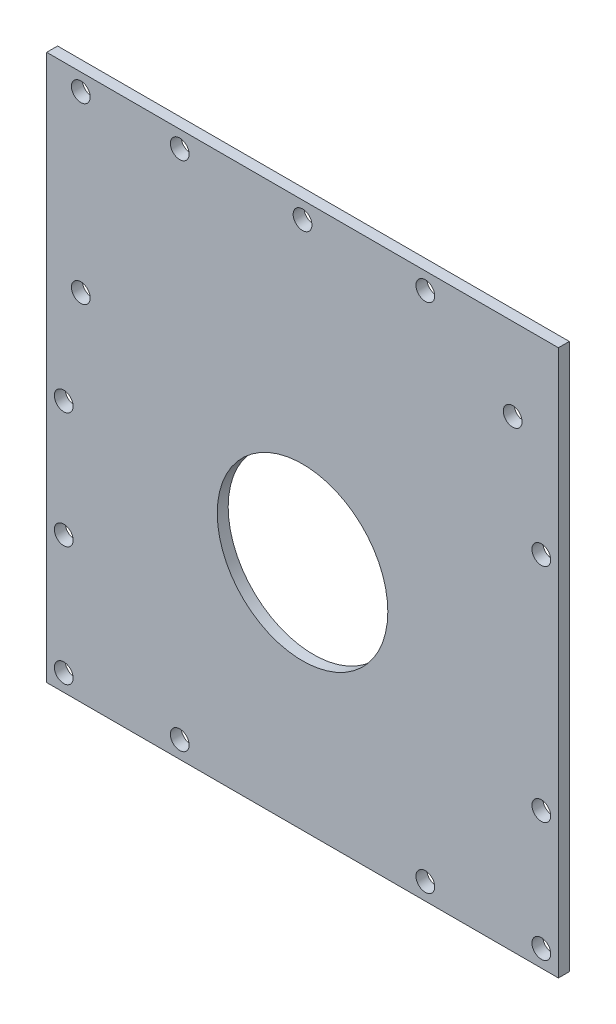
SolidWorks part; units mm, degrees
material "AISI 304"
ref_plane "Front Plane" through (0, 0, 0) normal (0, 0, 1) x (1, 0, 0)
ref_plane "Top Plane" through (0, 0, 0) normal (0, 1, 0) x (1, 0, 0)
ref_plane "Right Plane" through (0, 0, 0) normal (1, 0, 0) x (0, 0, -1)
sketch "Sketch1" plane through (0, 0, 0) normal (0, 0, 1) x (1, 0, 0)
  line L0 (-75, 80) -> (75, -80) construction
  line L1 (-75, 80) -> (75, 80)
  line L2 (-75, 80) -> (-75, -80)
  line L3 (-75, -80) -> (75, -80)
  line L4 (75, 80) -> (75, -80)
  point P0 (0, 0)
  point P6 (0, 0)
  dimension "D1" = 150
  dimension "D2" = 160
extrude "Boss-Extrude1" add sketch "Sketch1" along normal blind 3.2
sketch "Sketch2" plane through (0, 0, 3.2) normal (0, 0, 1) x (1, 0, 0)
  line L0 (0, -12) -> (0, -47.5) construction
  line L3 (-75, -80) -> (75, -80) construction
  circle A1 centre (0, -12) radius 25
  dimension "D1" = 35.5
  dimension "D3" = 25
  dimension "D4" = 68
extrude "Cut-Extrude1" cut sketch "Sketch2" against normal up to next
sketch "Sketch4" plane through (0, 0, 3.2) normal (0, 0, 1) x (1, 0, 0)
  line L1 (-75, 68.5917) -> (-2.1136, 63.6666) construction
  line L3 (-15.844, 37.0022) -> (-75, 32.3611) construction
  line L4 (-18.745, 35.9674) -> (-15.844, 37.0022) construction
  spline S1 degree 3 poles (-2.1136, 63.6666) (2.6479, 63.5435) (7.3732, 62.9696) (16.586, 60.9588) (21.0732, 59.5219) (29.6553, 55.8535) (33.75, 53.622) (41.4098, 48.4598) (44.9747, 45.5292) (51.4594, 39.0872) (54.379, 35.5759) (59.4827, 28.1094) (61.6668, 24.1543) (65.2376, 15.9498) (66.6242, 11.7006) (68.5678, 3.0651) (69.1247, -1.321) (69.407, -10.0716) (69.1323, -14.4359) (67.7793, -22.9884) (66.701, -27.1763) (63.7966, -35.2312) (61.9706, -39.0979) (57.6525, -46.38) (55.1604, -49.7953) (49.6136, -56.0632) (46.5591, -58.9158) (40.0087, -63.9697) (36.513, -66.1711) (29.2148, -69.8593) (25.4125, -71.3461) (17.6434, -73.569) (13.6769, -74.3052) (5.7242, -75.0182) (1.7384, -74.9951) (-6.1106, -74.2087) (-9.9735, -73.4455) (-17.4419, -71.2236) (-21.0473, -69.7652) (-27.8787, -66.2219) (-31.1045, -64.1372) (-37.0713, -59.4311) (-39.8121, -56.8099) (-44.7234, -51.1376) (-46.8938, -48.0866) (-50.6012, -41.6745) (-52.1382, -38.3135) (-54.5405, -31.409) (-55.4057, -27.8657) (-56.4508, -20.7276) (-56.6309, -17.133) (-56.3173, -10.0219) (-55.8238, -6.5057) (-54.1987, 0.3254) (-53.0672, 3.64) (-50.224, 9.9549) (-48.5122, 12.955) (-44.5854, 18.5423) (-42.3705, 21.1295) (-37.5304, 25.8099) (-34.9053, 27.9031) (-29.3504, 31.5347) (-26.4206, 33.0731) (-21.867, 34.9417) (-20.3144, 35.493) (-18.745, 35.9674) knots 0 0 0 0 0.03125 0.03125 0.0625 0.0625 0.09375 0.09375 0.125 0.125 0.15625 0.15625 0.1875 0.1875 0.21875 0.21875 0.25 0.25 0.28125 0.28125 0.3125 0.3125 0.34375 0.34375 0.375 0.375 0.40625 0.40625 0.4375 0.4375 0.46875 0.46875 0.5 0.5 0.53125 0.53125 0.5625 0.5625 0.59375 0.59375 0.625 0.625 0.65625 0.65625 0.6875 0.6875 0.71875 0.71875 0.75 0.75 0.78125 0.78125 0.8125 0.8125 0.84375 0.84375 0.875 0.875 0.90625 0.90625 0.9375 0.9375 0.96875 0.96875 0.984535 0.984535 0.984535 0.984535 construction
sketch "Sketch3" plane through (0, 0, 0) normal (0, 0, -1) x (-1, 0, 0)
  line L1 (75, -80) -> (-75, -80) construction
  line L2 (75, 80) -> (75, -80) construction
  line L3 (-75, -80) -> (-75, 80) construction
  line L4 (-75, 80) -> (75, 80) construction
  line L5 (70, 80) -> (70, -80) construction
  circle A0 centre (65, 24) radius 2.75
  circle A1 centre (-70, -75) radius 2.75
  circle A2 centre (36, -75) radius 2.75
  circle A3 centre (-36, -75) radius 2.75
  circle A4 centre (70, -75) radius 2.75
  circle A5 centre (-70, -40) radius 2.75
  circle A6 centre (-70, 25) radius 2.75
  circle A7 centre (-36, 75) radius 2.75
  circle A8 centre (36, 75) radius 2.75
  circle A9 centre (65, 75) radius 2.75
  circle A10 centre (70, -40) radius 2.75
  circle A13 centre (70, -6) radius 2.75
  circle A14 centre (0, 75) radius 2.75
  circle A15 centre (-61.5928, 55.8759) radius 2.75
  dimension "D1" = 5.5
  dimension "D2" = 5.5
  dimension "D3" = 5.5
  dimension "D4" = 5.5
  dimension "D5" = 5.5
  dimension "D6" = 5.5
  dimension "D7" = 5.5
  dimension "D8" = 5.5
  dimension "D9" = 5.5
  dimension "D10" = 5.5
  dimension "D11" = 65
  dimension "D22" = 5.5
  dimension "D36" = 5
  dimension "D12" = 5
  dimension "D13" = 5
  dimension "D14" = 5
  dimension "D15" = 10
  dimension "D16" = 30
  dimension "D17" = 10
  dimension "D18" = 5
  dimension "D19" = 5
  dimension "D20" = 5
  dimension "D21" = 5
  dimension "D23" = 34
  dimension "D24" = 34
  dimension "D25" = 35
  dimension "D26" = 35
  dimension "D27" = 29
  dimension "D28" = 34
  dimension "D31" = 5
  dimension "D32" = 5
  dimension "D33" = 32
  dimension "D34" = 31.9488
  dimension "D35" = 5
extrude "Cut-Extrude2" cut sketch "Sketch3" against normal up to next
